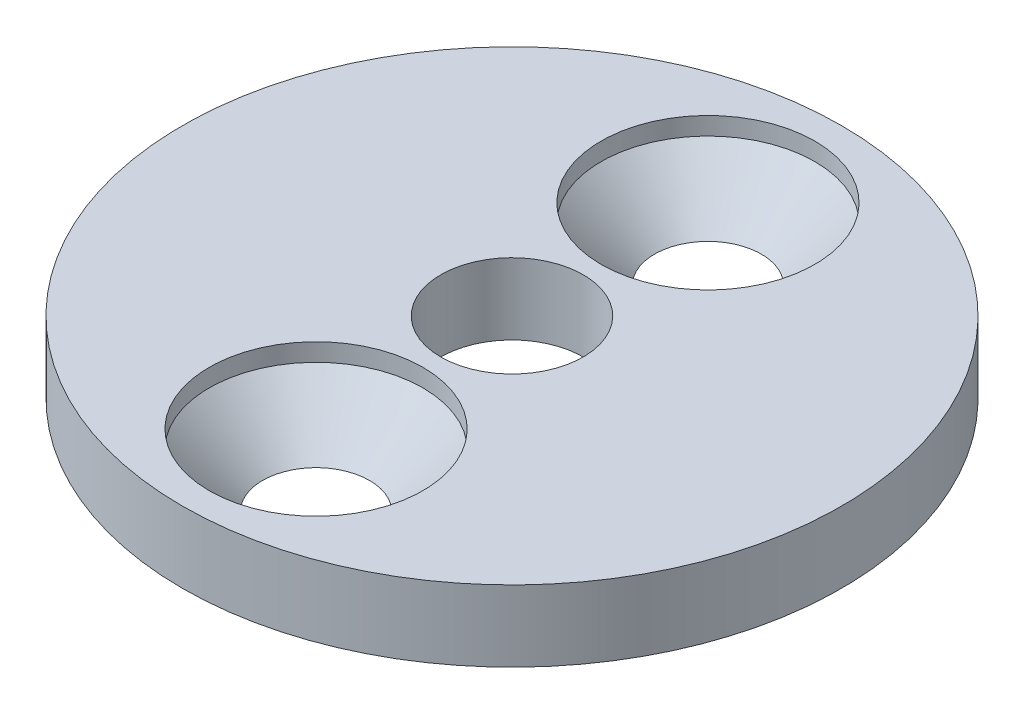
SolidWorks part; units mm, degrees
ref_plane "Front Plane" through (0, 0, 0) normal (0, 0, 1) x (1, 0, 0)
ref_plane "Top Plane" through (0, 0, 0) normal (0, 1, 0) x (1, 0, 0)
ref_plane "Right Plane" through (0, 0, 0) normal (1, 0, 0) x (0, 0, -1)
sketch "Sketch1" plane through (0, 0, 0) normal (0, 1, 0) x (1, 0, 0)
  circle A0 centre (0, 0) radius 9.25
  circle A1 centre (0, 0) radius 2
  dimension "D1" = 18.5
  dimension "D2" = 4
extrude "Boss-Extrude1" add sketch "Sketch1" along normal blind 2
sketch "Sketch4" plane through (0, 0, 0) normal (1, 0, 0) x (0, 0, -1)
  line L0 (5.5, 2) -> (5.5, 0) construction
  line L1 (9.25, 2) -> (-9.25, 2) construction
  line L2 (5.5, 0) -> (5.5, 2)
  line L3 (5.5, 2) -> (8.5, 2)
  line L4 (8.5, 2) -> (8.5, 1.5)
  line L5 (8.5, 1.5) -> (7, 0)
  line L6 (-9.25, 0) -> (9.25, 0) construction
  line L7 (7, 0) -> (5.5, 0)
  dimension "D1" = 5.5
  dimension "D2" = 3
  dimension "D3" = 1.5
  dimension "D4" = 45
revolve "Cut-Revolve1" cut sketch "Sketch4" angle 360 about L0
pattern_circular "CirPattern1" count 2 over 360 about axis through (0, 0, 0) along (0, 1, 0) of "Cut-Revolve1"
